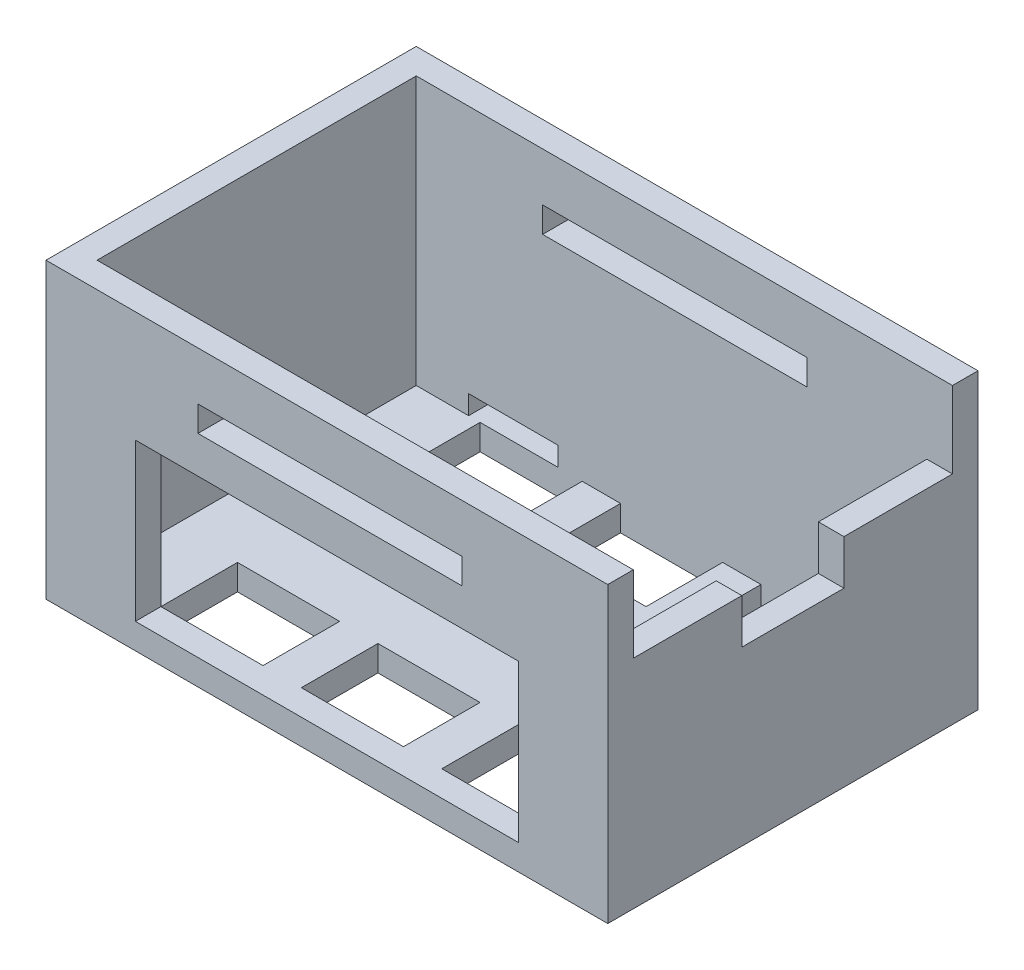
SolidWorks part; units mm, degrees
ref_plane "Front Plane" through (0, 0, 0) normal (0, 0, 1) x (1, 0, 0)
ref_plane "Top Plane" through (0, 0, 0) normal (0, 1, 0) x (1, 0, 0)
ref_plane "Right Plane" through (0, 0, 0) normal (1, 0, 0) x (0, 0, -1)
sketch "Sketch2" plane through (0, 0, 0) normal (0, 1, 0) x (1, 0, 0)
  line L1 (-22, 14.5) -> (22, 14.5)
  line L2 (-22, 14.5) -> (-22, -14.5)
  line L3 (-22, -14.5) -> (22, -14.5)
  line L4 (22, 14.5) -> (22, -14.5)
  line L5 (-22, 14.5) -> (22, -14.5) construction
  line L6 (-22, -14.5) -> (22, 14.5) construction
  point P0 (0, 0)
extrude "Boss-Extrude1" add sketch "Sketch2" along normal blind 23
sketch "Sketch3" plane through (0, 23, 0) normal (0, 1, 0) x (1, 0, 0)
  line L5 (-20, 12.5) -> (20, 12.5)
  line L6 (-20, 12.5) -> (-20, -12.5)
  line L7 (-20, -12.5) -> (20, -12.5)
  line L8 (20, 12.5) -> (20, -12.5)
  line L9 (-20, 12.5) -> (20, -12.5) construction
  line L10 (-20, -12.5) -> (20, 12.5) construction
  point P0 (0, 0)
  point P1 (0, 0)
extrude "Cut-Extrude1" cut sketch "Sketch3" against normal blind 21 contours L6 L5 L8 L7
sketch "Sketch4" plane through (0, 0, 14.5) normal (0, 0, 1) x (1, 0, 0)
  line L0 (-22, 23) -> (-20.1, 23) construction
  line L1 (-22, 23) -> (22, 23) construction
  line L2 (-20.1, 23) -> (-10.1, 23) construction
  line L3 (-10.1, 23) -> (-10.1, 17.2) construction
  line L4 (-10.1, 17.2) -> (10.6, 17.2) construction
  line L5 (-10.1, 17.2) -> (10.6, 17.2)
  line L6 (-10.1, 17.2) -> (-10.1, 19.2)
  line L7 (10.6, 17.2) -> (10.6, 19.2)
  line L8 (-10.1, 19.2) -> (10.6, 19.2)
  line L10 (-20.1, 23) -> (-20.1, 2) construction
  line L11 (-20.1, 2) -> (-15.1, 2) construction
  line L12 (20.2, 2) -> (20.2, 23) construction
  line L13 (-15.1, 2) -> (-15.1, 14.3) construction
  line L14 (-15.1, 14.3) -> (14.9, 14.3) construction
  line L16 (-15.1, 2) -> (14.9, 2)
  line L17 (-15.1, 2) -> (-15.1, 14.3)
  line L18 (-15.1, 14.3) -> (14.9, 14.3)
  line L19 (14.9, 2) -> (14.9, 14.3)
extrude "Cut-Extrude2" cut sketch "Sketch4" against normal blind 33 contours L5 L6 L8 L7
sketch "Sketch5" plane through (0, 0, 14.5) normal (0, 0, 1) x (1, 0, 0)
  line L0 (-22, 23) -> (-20, 23) construction
  line L1 (-22, 23) -> (22, 23) construction
  line L2 (-20, 23) -> (-20, 2) construction
  line L3 (-20, 2) -> (-15, 2) construction
  line L4 (-15, 2) -> (-15, 14.3) construction
  line L5 (-15, 14.3) -> (15, 14.3) construction
  line L7 (-15, 2) -> (15, 2)
  line L8 (-15, 2) -> (-15, 14.3)
  line L9 (-15, 14.3) -> (15, 14.3)
  line L10 (15, 2) -> (15, 14.3)
extrude "Cut-Extrude3" cut sketch "Sketch5" against normal blind 2
sketch "Sketch8" plane through (22, 0, 0) normal (1, 0, 0) x (0, 0, -1)
  line L0 (-14.5, 23) -> (-12.5, 23) construction
  line L1 (-14.5, 23) -> (14.5, 23) construction
  line L2 (-12.5, 17) -> (-4, 17)
  line L3 (-12.5, 23) -> (-12.5, 17) construction
  line L4 (-12.5, 17) -> (12.5, 17) construction
  line L5 (0, 17) -> (0, 15.25) construction
  line L6 (-12.5, 23) -> (12.5, 23)
  line L7 (-12.5, 23) -> (-12.5, 17)
  line L9 (12.5, 23) -> (12.5, 17)
  line L10 (4, 17) -> (12.5, 17)
  line L11 (-4, 13.5) -> (4, 13.5)
  line L12 (-4, 13.5) -> (-4, 17)
  line L14 (4, 13.5) -> (4, 17)
  line L15 (-4, 13.5) -> (4, 17) construction
  line L16 (-4, 17) -> (4, 13.5) construction
extrude "Cut-Extrude5" cut sketch "Sketch8" against normal blind 2
sketch "Sketch11" plane through (0, 0, -14.5) normal (0, 0, -1) x (-1, 0, 0)
  line L0 (-22, 0) -> (-22, 2) construction
  line L1 (-22, 23) -> (-22, 0) construction
  line L2 (-22, 2) -> (-16.1, 2) construction
  line L3 (-22, 2) -> (-20, 2) construction
  line L4 (-20, 2) -> (-16.1, 2)
  line L5 (-20, 2) -> (-20, 10.6)
  line L6 (-16.1, 2) -> (-16.1, 10.6)
  line L7 (-20, 10.6) -> (-16.1, 10.6)
  line L8 (-16.1, 2) -> (8.9, 2) construction
  line L10 (8.9, 2) -> (15.9, 2)
  line L11 (8.9, 2) -> (8.9, 3.5)
  line L12 (8.9, 3.5) -> (15.9, 3.5)
  line L13 (15.9, 2) -> (15.9, 3.5)
extrude "Cut-Extrude6" cut sketch "Sketch11" against normal blind 2
sketch "Sketch12" plane through (22, 0, 0) normal (1, 0, 0) x (0, 0, -1)
  line L0 (-12.5, 17) -> (-12.5, 2) construction
  line L1 (-12.5, 2) -> (-12.5, 10) construction
  line L2 (-12.5, 2) -> (-12.5, 23) construction
  line L3 (-12.5, 2) -> (12.5, 2) construction
  line L4 (12.5, 2) -> (12.5, 17) construction
  line L9 (-12.5, 6) -> (-12.5, 14)
  line L10 (-12.5, 14) -> (-10.5, 14)
  line L17 (-12.5, 6) -> (-10.5, 6)
  line L18 (-10.5, 14) -> (-10.5, 6)
  line L19 (-12.5, 10) -> (-10.5, 6) construction
  line L20 (-12.5, 10) -> (-10.5, 14) construction
  line L21 (0, 2) -> (0, 6) construction
  line L22 (12.5, 6) -> (12.5, 14)
  line L23 (12.5, 14) -> (10.5, 14)
  line L24 (10.5, 14) -> (10.5, 6)
  line L25 (12.5, 6) -> (10.5, 6)
  dimension "D1" = 4
sketch "Sketch13" plane through (0, 2, 0) normal (0, 1, 0) x (1, 0, 0)
  line L0 (-15, -12.5) -> (15, -12.5) construction
  line L6 (-20, -12.5) -> (-15, -12.5) construction
  line L7 (-20, -12.5) -> (-15, -12.5) construction
  line L8 (0, 0) -> (5, 0) construction
  line L13 (-7, -12.5) -> (-4, -12.5) construction
  line L14 (-15, -12.5) -> (-7, -12.5)
  line L15 (-15, -12.5) -> (-15, -6.5)
  line L16 (-15, -6.5) -> (-7, -6.5)
  line L17 (-7, -12.5) -> (-7, -6.5)
  line L18 (4, -12.5) -> (7, -12.5) construction
  line L19 (-4, -12.5) -> (4, -12.5)
  line L20 (-4, -12.5) -> (-4, -6.5)
  line L21 (-4, -6.5) -> (4, -6.5)
  line L22 (4, -12.5) -> (4, -6.5)
  line L23 (7, 6.5) -> (15, 6.5)
  line L24 (7, -12.5) -> (15, -12.5)
  line L25 (7, -12.5) -> (7, -6.5)
  line L26 (7, -6.5) -> (15, -6.5)
  line L27 (15, -12.5) -> (15, -6.5)
  line L28 (15, 12.5) -> (15, 6.5)
  line L29 (7, 12.5) -> (15, 12.5)
  line L30 (7, 12.5) -> (7, 6.5)
  line L31 (-15, 6.5) -> (-7, 6.5)
  line L32 (-7, 12.5) -> (-7, 6.5)
  line L33 (-15, 12.5) -> (-7, 12.5)
  line L34 (-15, 12.5) -> (-15, 6.5)
  line L35 (-4, 6.5) -> (4, 6.5)
  line L36 (4, 12.5) -> (4, 6.5)
  line L37 (-4, 12.5) -> (4, 12.5)
  line L38 (-4, 12.5) -> (-4, 6.5)
extrude "Cut-Extrude8" cut sketch "Sketch13" against normal blind 2 contours L16 L17 L14 L15 | L22 L21 L20 L19 | L25 L24 L27 L26 | L23 L28 L29 L30 | L35 L36 L37 L38 | L31 L32 L33 L34
